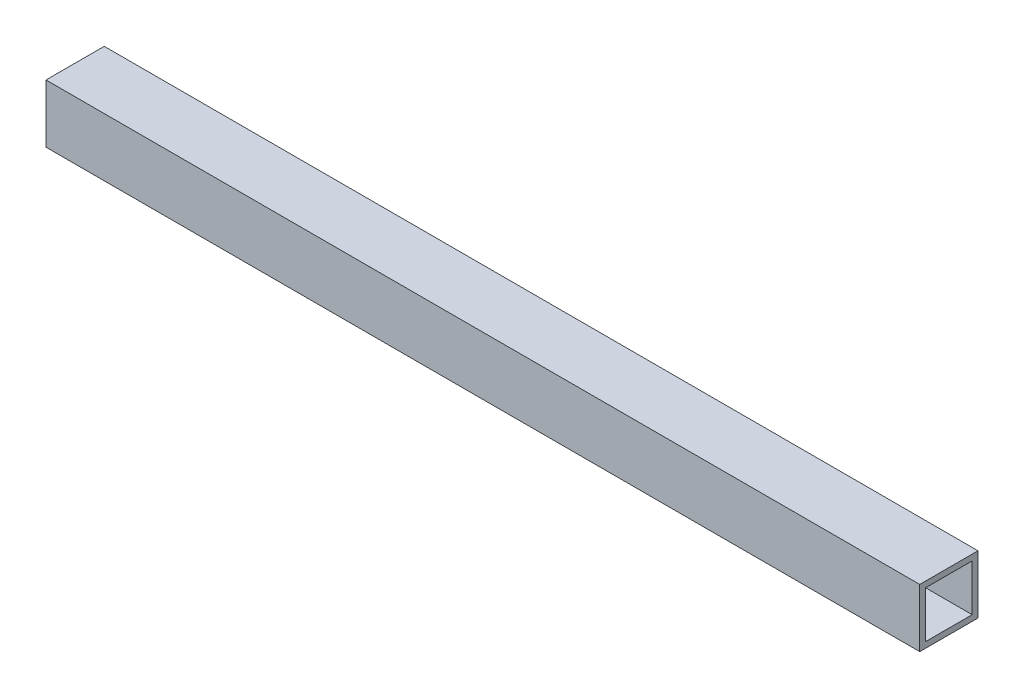
SolidWorks part; units mm, degrees
material "Stainless Steel (ferritic)"
ref_plane "Front Plane" through (0, 0, 0) normal (0, 0, 1) x (1, 0, 0)
ref_plane "Top Plane" through (0, 0, 0) normal (0, 1, 0) x (1, 0, 0)
ref_plane "Right Plane" through (0, 0, 0) normal (1, 0, 0) x (0, 0, -1)
sketch "Sketch1" plane through (0, 0, 0) normal (1, 0, 0) x (0, 0, -1)
  line L0 (-4, 4) -> (4, 4)
  line L1 (-5, -5) -> (5, -5)
  line L2 (-5, -5) -> (-5, 5)
  line L3 (-5, 5) -> (5, 5)
  line L4 (5, -5) -> (5, 5)
  line L5 (-5, -5) -> (5, 5) construction
  line L6 (-5, 5) -> (5, -5) construction
  line L7 (4, -4) -> (4, 4)
  line L8 (-4, -4) -> (4, -4)
  line L9 (-4, -4) -> (-4, 4)
  point P0 (0, 0)
  dimension "D1" = 10
  dimension "D2" = 10
  dimension "D3" = 1
extrude "Boss-Extrude1" add sketch "Sketch1" along normal blind 150
